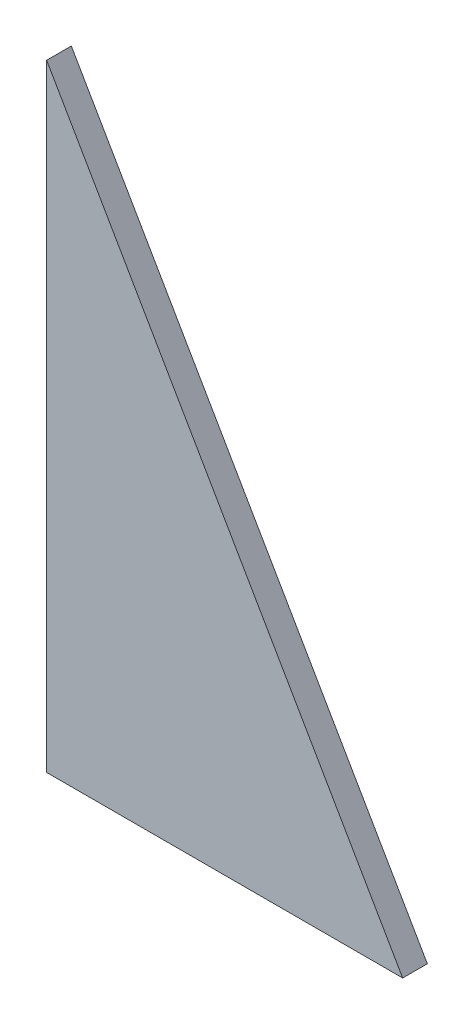
SolidWorks part; units mm, degrees
material "Thornel Mat VMA"
ref_plane "Front Plane" through (0, 0, 0) normal (0, 0, 1) x (1, 0, 0)
ref_plane "Top Plane" through (0, 0, 0) normal (0, 1, 0) x (1, 0, 0)
ref_plane "Right Plane" through (0, 0, 0) normal (1, 0, 0) x (0, 0, -1)
sketch "Sketch1" plane through (0, 0, 0) normal (0, 0, 1) x (1, 0, 0)
  line L0 (0, 63.5) -> (36.6522, 0)
  line L1 (0, 0) -> (36.6522, 0)
  line L2 (0, 0) -> (0, 63.5)
extrude "Extrude1" add sketch "Sketch1" along normal blind 2.54
sketch "Sketch2" plane through (0, 0, 0) normal (-1, 0, 0) x (0, 0, 1)
  line L0 (0, 31.75) -> (2.54, 31.75) construction
  line L1 (0, 63.5) -> (0, 0) construction
  line L2 (2.54, 63.5) -> (2.54, 0) construction
sketch "Sketch4" plane through (0, 0, 0) normal (0, 0, -1) x (-1, 0, 0)
  line L0 (0, 31.75) -> (0, 35.306)
  line L1 (0, 63.5) -> (0, 0) construction
  line L2 (0, 31.75) -> (0, 28.194)
  line L3 (0, 35.306) -> (-10.668, 35.306)
  line L4 (0, 28.194) -> (-10.668, 28.194)
  line L5 (-10.668, 35.306) -> (-10.668, 28.194)
extrude "Extrude3" cut sketch "Sketch4" against normal blind 2.032
sketch "Sketch3" plane through (0, 0, 0) normal (0, 0, -1) x (-1, 0, 0)
  line L0 (0, 31.75) -> (-2.54, 31.75) construction
  line L1 (-2.54, 31.75) -> (-2.54, 20.955)
  line L2 (0, 28.194) -> (0, 35.306) construction
  line L3 (-2.54, 42.545) -> (-2.54, 31.75)
  line L4 (-2.54, 42.545) -> (-6.8542, 42.545)
  line L5 (-2.54, 20.955) -> (-19.3159, 20.955)
  line L6 (-6.8542, 42.545) -> (-19.3159, 20.955)
  line L7 (-36.6522, 0) -> (0, 63.5) construction
extrude "Extrude2" cut sketch "Sketch3" against normal blind 0.9144
fillet "Fillet1" radius 1.5875 6 edges at (2.54, 20.955, 0.4572) (10.668, 35.306, 1.4732) (10.668, 28.194, 1.4732) (19.3159, 20.955, 0.4572) (6.8542, 42.545, 0.4572) (2.54, 42.545, 0.4572)
